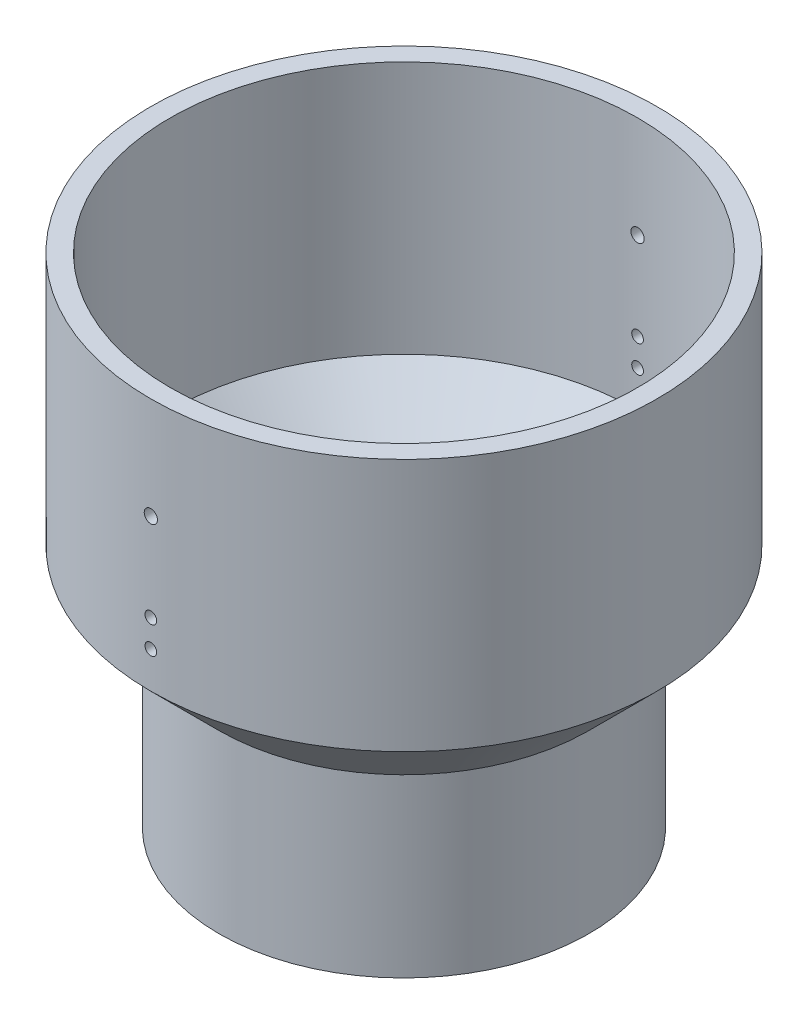
SolidWorks part; units mm, degrees
ref_plane "Front Plane" through (0, 0, 0) normal (0, 0, 1) x (1, 0, 0)
ref_plane "Top Plane" through (0, 0, 0) normal (0, 1, 0) x (1, 0, 0)
ref_plane "Right Plane" through (0, 0, 0) normal (1, 0, 0) x (0, 0, -1)
sketch "Sketch1" plane through (0, 0, 0) normal (0, 0, 1) x (1, 0, 0)
  line L0 (65, -65) -> (47.5, -82.5)
  line L2 (65, 0) -> (65, -65)
  line L4 (47.5, -82.5) -> (47.5, -127.6795)
  line L14 (42.5, -127.6795) -> (47.5, -127.6795)
  line L15 (60, -65) -> (60, 0)
  line L16 (60, -65) -> (42.5, -82.5)
  line L17 (42.5, -82.5) -> (42.5, -127.6795)
  line L20 (0, 0) -> (65, 0) construction
  line L21 (60, 0) -> (65, 0)
  line L22 (0, 0) -> (0, -70.7807) construction
  dimension "D1" = 65
  dimension "D2" = 45.1795
  dimension "D3" = 135
  dimension "D4" = 5
  dimension "D5" = 65
  dimension "D6" = 17.5
revolve "Revolve1" add sketch "Sketch1" angle 360 about L22
ref_plane "Plane3" through (0, 0, -65) normal (0, 0, 1) x (1, 0, 0)
sketch "Sketch7" plane through (0, 0, -65) normal (0, 0, 1) x (1, 0, 0)
  line L0 (65, 0) -> (-65, 0) construction
  circle A0 centre (0, -48.62) radius 1.5
  circle A1 centre (0, -55.62) radius 1.5
  circle A2 centre (0, -26.08) radius 1.7
  point P6 (0, 0)
  dimension "D2" = 7
  dimension "D3" = 3.4
  dimension "D4" = 3
  dimension "D5" = 0
  dimension "D1" = 48.62
  dimension "D6" = 26.08
extrude "Cut-Extrude2" cut sketch "Sketch7" along normal through all
